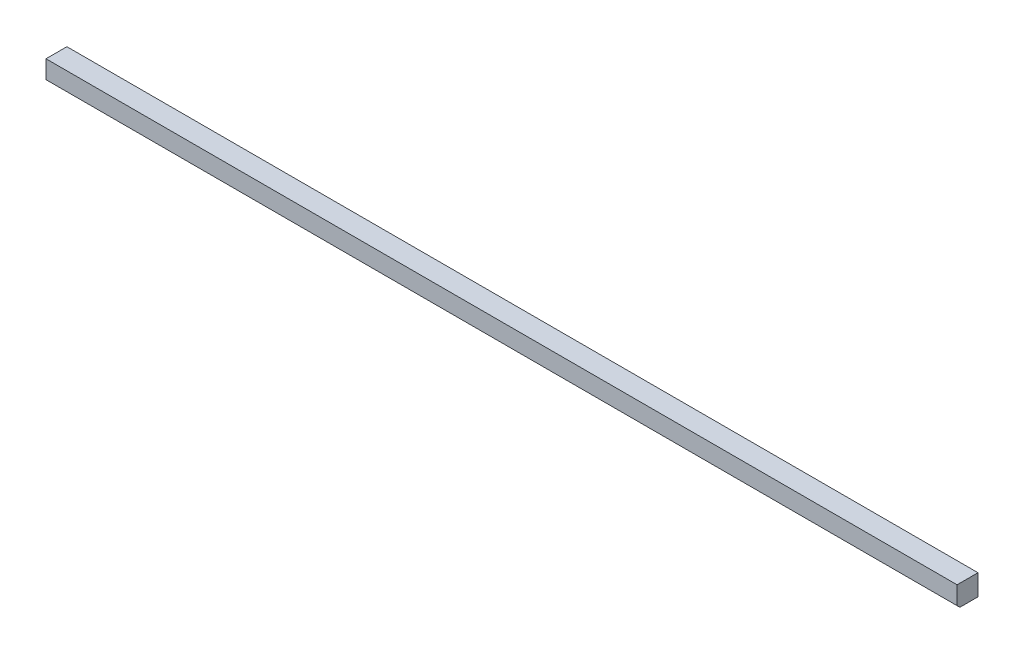
SolidWorks part; units mm, degrees
material "Oak"
ref_plane "Front Plane" through (0, 0, 0) normal (0, 0, 1) x (1, 0, 0)
ref_plane "Top Plane" through (0, 0, 0) normal (0, 1, 0) x (1, 0, 0)
ref_plane "Right Plane" through (0, 0, 0) normal (1, 0, 0) x (0, 0, -1)
sketch "Sketch1" plane through (0, 0, 0) normal (0, 1, 0) x (1, 0, 0)
  line L1 (0, 0) -> (830.2752, 0)
  line L2 (0, 0) -> (0, 19.05)
  line L3 (0, 19.05) -> (830.2752, 19.05)
  line L4 (830.2752, 0) -> (830.2752, 19.05)
  dimension "D1" = 19.05
  dimension "D2" = 830.2752
extrude "Boss-Extrude1" add sketch "Sketch1" along normal blind 19.05
chamfer "Chamfer1" distance 2.54 angle 45 1 edges at (415.1376, 0, 0)
